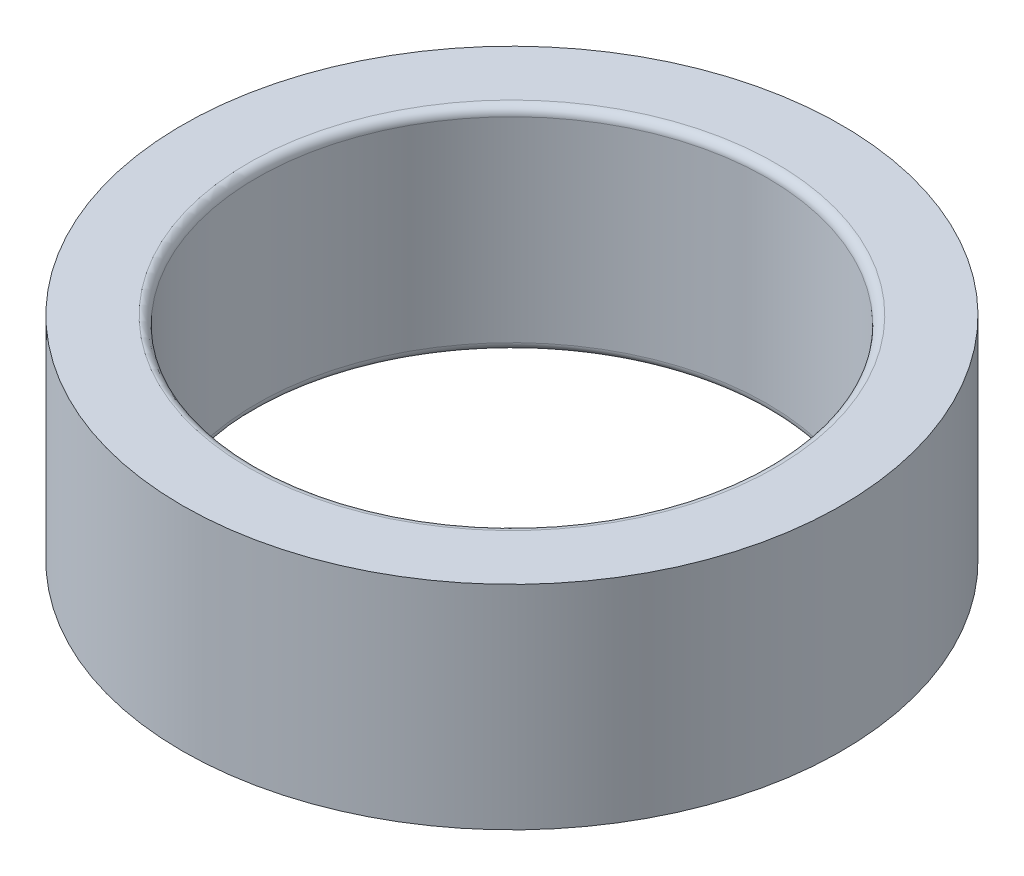
SolidWorks part; units mm, degrees
ref_plane "Front Plane" through (0, 0, 0) normal (0, 0, 1) x (1, 0, 0)
ref_plane "Top Plane" through (0, 0, 0) normal (0, 1, 0) x (1, 0, 0)
ref_plane "Right Plane" through (0, 0, 0) normal (1, 0, 0) x (0, 0, -1)
sketch "Sketch1" plane through (0, 0, 0) normal (0, 1, 0) x (1, 0, 0)
  circle A0 centre (0, 0) radius 7.75
  circle A1 centre (0, 0) radius 6
  dimension "D1" = 15.5
  dimension "D2" = 12
extrude "Boss-Extrude1" add sketch "Sketch1" along normal blind 5
fillet "Fillet1" radius 0.2 2 edges at (0, 0, 6) (0, 5, 6)
